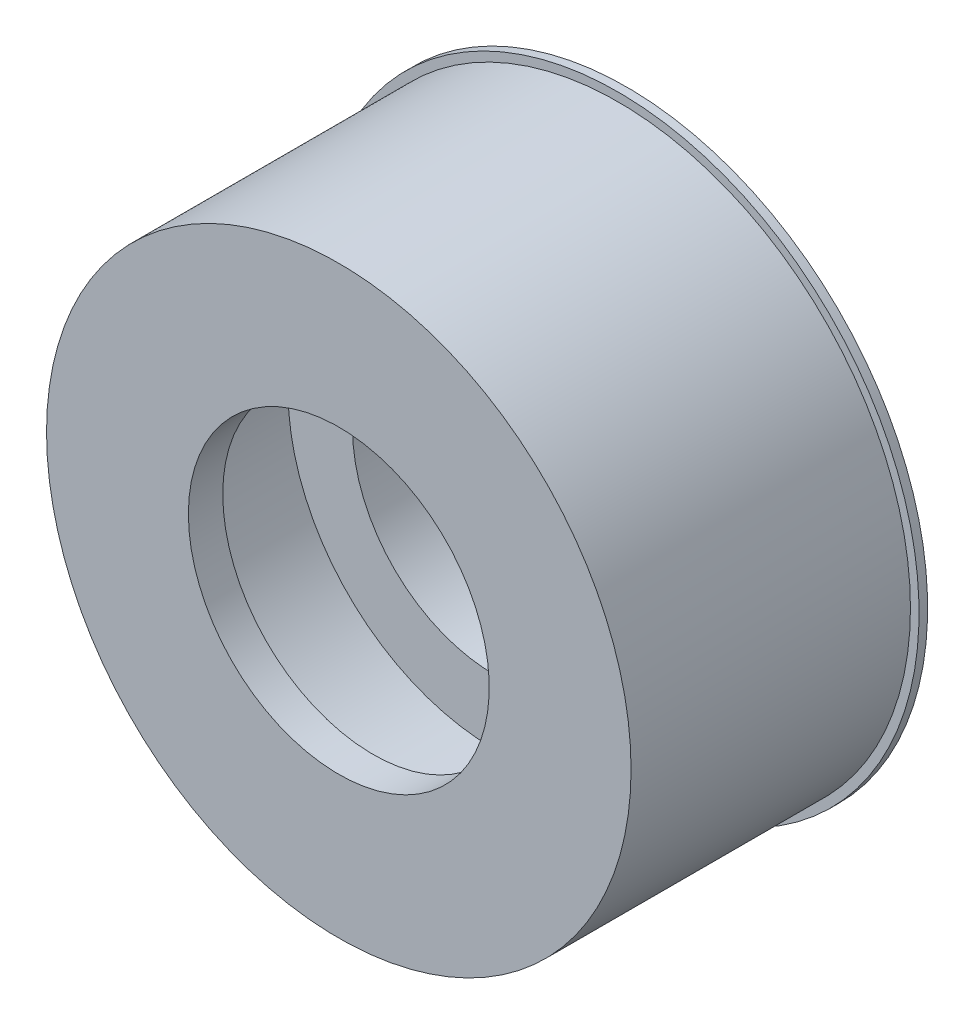
SolidWorks part; units mm, degrees
ref_plane "Front Plane" through (0, 0, 0) normal (0, 0, 1) x (1, 0, 0)
ref_plane "Top Plane" through (0, 0, 0) normal (0, 1, 0) x (1, 0, 0)
ref_plane "Right Plane" through (0, 0, 0) normal (1, 0, 0) x (0, 0, -1)
sketch "Sketch2" plane through (0, 0, 0) normal (0, 1, 0) x (1, 0, 0)
  line L0 (-3.5, -6.7) -> (-3.5, -5.9)
  line L1 (-3.5, -5.9) -> (-4.8, -5.58)
  line L2 (-4.8, -5.58) -> (-4.8, -3.08)
  line L3 (-4.8, -3.08) -> (-3.3, -3.08)
  line L4 (-3.3, -3.08) -> (-3.3, -1)
  line L5 (-3.3, -1) -> (-5, -1)
  line L6 (-3.5, -6.7) -> (-6.8, -6.7)
  line L7 (-6.8, -6.7) -> (-6.8, -0.2)
  line L8 (-5, -1) -> (-5, -0.4)
  line L9 (-5, -0.4) -> (-5.3, -0.4)
  line L10 (-5.3, -0.4) -> (-5.3, 0)
  line L11 (-5.3, 0) -> (-7, 0)
  line L12 (-7, 0) -> (-7, -0.2)
  line L13 (-7, -0.2) -> (-6.8, -0.2)
  line L14 (0, 0) -> (0, -6.7) construction
  line L15 (7, -0.2) -> (6.8, -0.2) construction
  line L16 (7, 0) -> (7, -0.2) construction
  line L17 (5.3, 0) -> (7, 0) construction
  line L18 (5.3, -0.4) -> (5.3, 0) construction
  line L19 (5, -0.4) -> (5.3, -0.4) construction
  line L20 (5, -1) -> (5, -0.4) construction
  line L21 (6.8, -6.7) -> (6.8, -0.2) construction
  line L22 (3.5, -6.7) -> (6.8, -6.7) construction
  line L23 (3.3, -1) -> (5, -1) construction
  line L24 (3.3, -3.08) -> (3.3, -1) construction
  line L25 (4.8, -3.08) -> (3.3, -3.08) construction
  line L26 (4.8, -5.58) -> (4.8, -3.08) construction
  line L27 (3.5, -5.9) -> (4.8, -5.58) construction
  line L28 (3.5, -6.7) -> (3.5, -5.9) construction
  point P2 (0, 0)
  point P32 (-5.6144, -37.3097)
  point P33 (6.9619, -36.9573)
  point P34 (0, 0)
  point P35 (0, 0)
  point P36 (-3.5, -39.2112)
  point P37 (5.3, -1.9452)
  point P38 (-4.3628, -25.418)
  point P39 (-12.2546, -31.118)
  point P40 (-7.9146, -11.9112)
  point P41 (-5.3, -0.5355)
  point P42 (-6.4622, -11.4882)
  point P43 (-4.4008, -5.7492)
  point P44 (-5.3, 0)
  point P45 (-3.3, -5.3924)
other "AlignGroup1"
other "AlignGroup2" parameters "D1"=6.1239, "D2"=15.6, "D3"=6.4543, "D4"=0.8, "D5"=10.0543, "D6"=6, "D7"=8.1501, "D8"=3.5773, "D9"=31.118, "D10"=2.5, "D11"=0.8, "D12"=5.3492, "D13"=1.7, "D14"=0.819, "D15"=0.3
revolve "Revolve1" add sketch "Sketch2" angle 360 about L14
